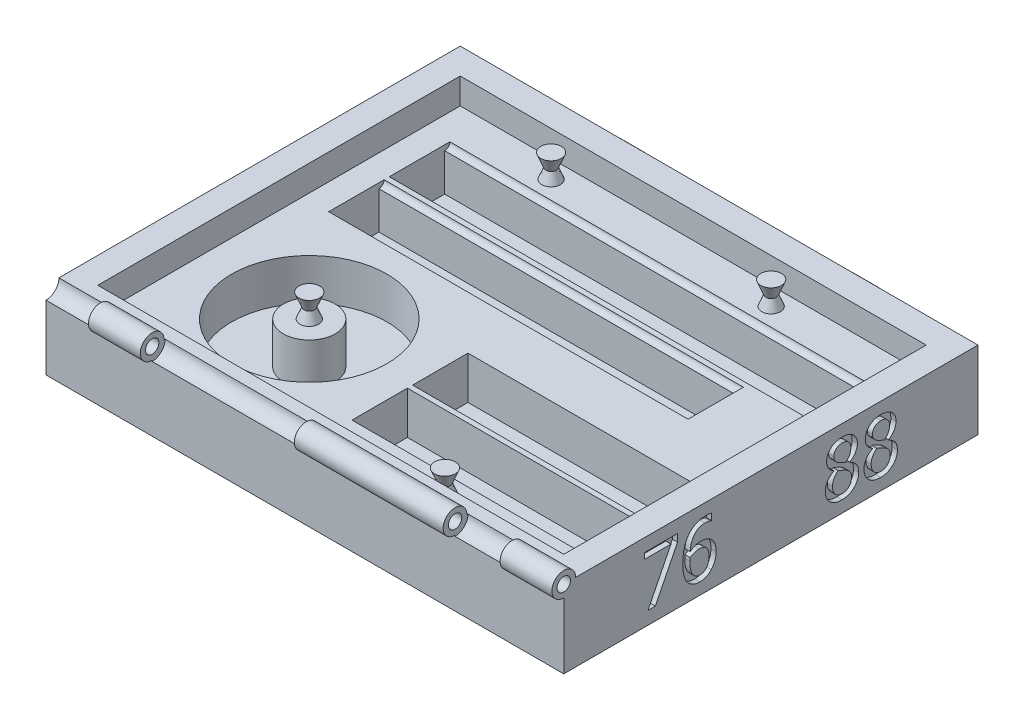
SolidWorks part; units mm, degrees
ref_plane "Front Plane" through (0, 0, 0) normal (0, 0, 1) x (1, 0, 0)
ref_plane "Top Plane" through (0, 0, 0) normal (0, 1, 0) x (1, 0, 0)
ref_plane "Right Plane" through (0, 0, 0) normal (1, 0, 0) x (0, 0, -1)
sketch "Sketch1" plane through (0, 0, 0) normal (0, 0, 1) x (1, 0, 0)
  line L0 (0, 0) -> (254, 0)
  line L1 (254, 0) -> (254, 101.6)
  line L2 (0, 0) -> (0, 101.6)
  line L3 (0, 101.6) -> (12.7, 101.6)
  line L4 (12.7, 101.6) -> (12.7, 25.4)
  line L5 (12.7, 25.4) -> (241.3, 25.4)
  line L6 (241.3, 25.4) -> (241.3, 101.6)
  line L7 (241.3, 101.6) -> (254, 101.6)
extrude "Boss-Extrude1" add sketch "Sketch1" along normal blind 177.8
sketch "Sketch2" plane through (0, 25.4, 0) normal (0, 1, 0) x (1, 0, 0)
  line L0 (228.6, -20.32) -> (25.4, -20.32)
  line L1 (241.3, -177.8) -> (12.7, -177.8) construction
  line L2 (241.3, 0) -> (12.7, 0) construction
  line L3 (228.6, -47.498) -> (228.6, -20.32)
  line L4 (25.4, -47.498) -> (228.6, -47.498)
  line L9 (201.676, -52.578) -> (25.4, -52.578)
  line L10 (201.676, -52.578) -> (201.676, -77.216)
  line L11 (201.676, -77.216) -> (25.4, -77.216)
  line L13 (228.6, -103.124) -> (119.634, -103.124)
  line L14 (228.6, -103.124) -> (228.6, -127.762)
  line L15 (228.6, -127.762) -> (119.634, -127.762)
  line L16 (25.4, -47.498) -> (25.4, -20.32)
  line L19 (228.6, -132.842) -> (119.634, -132.842)
  line L20 (228.6, -132.842) -> (228.6, -157.48)
  line L21 (25.4, -52.578) -> (25.4, -77.216)
  line L22 (119.634, -103.124) -> (119.634, -127.762)
  line L23 (119.634, -132.842) -> (119.634, -157.48)
  line L24 (119.634, -157.48) -> (228.6, -157.48)
  dimension "D1" = 5.08
  dimension "D2" = 20.32
  dimension "D3" = 5.08
  dimension "D4" = 20.32
  dimension "D5" = 0
extrude "Cut-Extrude1" cut sketch "Sketch2" against normal blind 12.7
sketch "Sketch3" plane through (228.6, 0, 0) normal (-1, 0, 0) x (0, 0, 1)
  circle A0 centre (157.48, 25.4) radius 3.81
  circle A1 centre (127.762, 25.4) radius 3.81
extrude "Cut-Extrude2" cut sketch "Sketch3" along normal blind 108.966
sketch "Sketch4" plane through (228.6, 0, 0) normal (-1, 0, 0) x (0, 0, 1)
  circle A0 centre (20.32, 25.4) radius 3.81
extrude "Cut-Extrude3" cut sketch "Sketch4" along normal blind 203.2
sketch "Sketch5" plane through (201.676, 0, 0) normal (-1, 0, 0) x (0, 0, 1)
  circle A0 centre (52.578, 25.4) radius 3.81
extrude "Cut-Extrude4" cut sketch "Sketch5" along normal blind 176.276
sketch "Sketch6" plane through (0, 12.7, 0) normal (0, 1, 0) x (1, 0, 0)
  line L0 (119.634, -132.842) -> (228.6, -132.842)
  line L1 (228.6, -132.842) -> (228.6, -157.48)
  line L2 (228.6, -157.48) -> (119.634, -157.48)
  line L3 (119.634, -157.48) -> (119.634, -132.842)
extrude "Cut-Extrude5" cut sketch "Sketch6" against normal blind 8.255
sketch "Sketch9" plane through (228.6, 0, 0) normal (-1, 0, 0) x (0, 0, 1)
  line L0 (157.48, 21.59) -> (157.48, 25.4)
  line L1 (157.48, 25.4) -> (161.29, 25.4)
  line L2 (161.29, 25.4) -> (161.29, 21.59)
  line L3 (161.29, 21.59) -> (157.48, 21.59)
  line L4 (127.762, 21.59) -> (127.762, 25.4)
  line L5 (127.762, 25.4) -> (131.572, 25.4)
  line L6 (131.572, 25.4) -> (131.572, 21.59)
  line L7 (131.572, 21.59) -> (127.762, 21.59)
  line L8 (48.768, 25.4) -> (52.578, 25.4)
  line L9 (52.578, 25.4) -> (52.578, 21.59)
  line L10 (52.578, 21.59) -> (48.768, 21.59)
  line L11 (48.768, 21.59) -> (48.768, 25.4)
  line L12 (16.51, 25.4) -> (20.32, 25.4)
  line L13 (20.32, 25.4) -> (20.32, 21.59)
  line L14 (20.32, 21.59) -> (16.51, 21.59)
  line L15 (16.51, 21.59) -> (16.51, 25.4)
extrude "Boss-Extrude2" add sketch "Sketch9" along normal blind 211.328
sketch "Sketch10" plane through (228.6, 0, 0) normal (-1, 0, 0) x (0, 0, 1)
  circle A0 centre (157.48, 25.4) radius 2.54
extrude "Cut-Extrude6" cut sketch "Sketch10" along normal blind 108.966
sketch "Sketch11" plane through (228.6, 0, 0) normal (-1, 0, 0) x (0, 0, 1)
  circle A0 centre (127.762, 25.4) radius 2.54
extrude "Cut-Extrude7" cut sketch "Sketch11" along normal blind 108.966
sketch "Sketch12" plane through (201.676, 0, 0) normal (-1, 0, 0) x (0, 0, 1)
  circle A0 centre (52.578, 25.4) radius 2.54
extrude "Cut-Extrude8" cut sketch "Sketch12" along normal blind 176.276
sketch "Sketch13" plane through (228.6, 0, 0) normal (-1, 0, 0) x (0, 0, 1)
  circle A0 centre (20.32, 25.4) radius 2.54
extrude "Cut-Extrude9" cut sketch "Sketch13" along normal blind 203.2
sketch "Sketch14" plane through (0, 12.7, 0) normal (0, 1, 0) x (1, 0, 0)
  line L0 (119.634, -127.762) -> (119.634, -103.124)
  line L1 (119.634, -103.124) -> (228.6, -103.124)
  line L2 (228.6, -103.124) -> (228.6, -127.762)
  line L3 (228.6, -127.762) -> (119.634, -127.762)
  line L4 (25.4, -77.216) -> (25.4, -52.578)
  line L5 (201.676, -52.578) -> (25.4, -52.578) construction
  line L6 (25.4, -50.038) -> (25.4, -77.216) construction
  line L7 (25.4, -52.578) -> (201.676, -52.578)
  line L8 (201.676, -52.578) -> (201.676, -77.216)
  line L9 (201.676, -77.216) -> (25.4, -77.216)
  line L10 (25.4, -47.498) -> (25.4, -20.32)
  line L11 (25.4, -20.32) -> (228.6, -20.32)
  line L12 (228.6, -47.498) -> (228.6, -17.78) construction
  line L13 (228.6, -47.498) -> (228.6, -20.32) construction
  line L14 (228.6, -20.32) -> (228.6, -47.498)
  line L15 (228.6, -47.498) -> (25.4, -47.498)
extrude "Cut-Extrude10" cut sketch "Sketch14" against normal blind 8.255
sketch "Sketch15" plane through (0, 0, 177.8) normal (0, 0, 1) x (1, 0, 0)
  line L0 (12.7, 25.4) -> (12.7, 50.8)
  line L1 (12.7, 25.4) -> (12.7, 101.6) construction
  line L2 (12.7, 50.8) -> (-40.623, 50.8)
  line L3 (-40.623, 50.8) -> (-40.623, 124.5264)
  line L4 (-40.623, 124.5264) -> (294.3288, 124.5264)
  line L5 (294.3288, 124.5264) -> (294.3288, 50.8)
  line L6 (294.3288, 50.8) -> (12.7, 50.8)
  line M2 (0, 101.6) -> (0, 0)
  line M4 (254, 0) -> (254, 101.6)
  line M5 (254, 101.6) -> (241.3, 101.6)
  line M6 (241.3, 101.6) -> (241.3, 25.4)
  line M8 (12.7, 25.4) -> (12.7, 101.6)
  line M9 (12.7, 101.6) -> (0, 101.6)
extrude "Cut-Extrude11" cut sketch "Sketch15" against normal blind 379.73 and the other way blind 44.45 contours L6 L5 L4 L3 L2 M2 M9 M8 M6 M5 M4 | L2 M8 M9 M2 | L6 M4 M5 M6
sketch "Sketch16" plane through (254, 0, 0) normal (1, 0, 0) x (0, 0, -1)
  line L0 (-177.8, 0) -> (-190.5, 0)
  line L1 (-190.5, 0) -> (-190.5, 50.8)
  line L2 (-177.8, 50.8) -> (-190.5, 50.8)
  line L7 (0, 0) -> (0, 50.8)
  line L8 (0, 50.8) -> (-177.8, 50.8)
  line L9 (-177.8, 50.8) -> (-177.8, 0)
  line L10 (-177.8, 0) -> (0, 0)
  line L13 (-177.8, 50.8) -> (-177.8, 0)
  dimension "D1" = 0
extrude "Boss-Extrude3" add sketch "Sketch16" against normal blind 254
sketch "Sketch17" plane through (254, 0, 0) normal (1, 0, 0) x (0, 0, -1)
  line L0 (0, 50.8) -> (12.7, 50.8)
  line L1 (12.7, 50.8) -> (12.7, 0)
  line L2 (12.7, 0) -> (0, 0)
  line L7 (0, 0) -> (0, 50.8)
  line L8 (0, 50.8) -> (-190.5, 50.8)
  line L9 (-190.5, 50.8) -> (-190.5, 0)
  line L10 (-190.5, 0) -> (0, 0)
  line L11 (0, 0) -> (0, 50.8)
  dimension "D1" = 0
extrude "Boss-Extrude4" add sketch "Sketch17" against normal blind 254
sketch "Sketch18" plane through (254, 0, 0) normal (1, 0, 0) x (0, 0, -1)
  line L0 (-190.5, 50.8) -> (12.7, 50.8)
  line L1 (12.7, 50.8) -> (12.7, 38.1)
  line L2 (12.7, 0) -> (12.7, 50.8) construction
  line L3 (12.7, 38.1) -> (-190.5, 38.1)
  line L4 (-190.5, 50.8) -> (-190.5, 0) construction
  line L5 (-190.5, 38.1) -> (-190.5, 50.8)
extrude "Cut-Extrude12" cut sketch "Sketch18" against normal blind 254
sketch "Sketch25" plane through (254, 0, 0) normal (1, 0, 0) x (0, 0, -1)
  text T0 "76" font "Tahoma" height 25.4
  text T1 "88" font "Tahoma" height 25.4
extrude "Cut-Extrude13" cut sketch "Sketch25" against normal blind 2.54
sketch "Sketch26" plane through (254, 0, 0) normal (1, 0, 0) x (0, 0, -1)
  circle A0 centre (-190.5, 38.1) radius 6.35
extrude "Cut-Extrude14" cut sketch "Sketch26" against normal blind 309.626
sketch "Sketch27" plane through (254, 0, 0) normal (1, 0, 0) x (0, 0, -1)
  line L0 (-184.658, 38.1) -> (-182.6014, 38.1)
  line L1 (-184.15, 38.1) -> (12.7, 38.1) construction
  line L2 (-182.6014, 38.1) -> (-185.679, 31.4435)
  line L3 (-185.679, 31.4435) -> (-190.5, 30.744)
  line L4 (-190.5, 31.75) -> (-190.5, 0) construction
  line L5 (-190.5, 30.744) -> (-190.5, 32.258)
  circle A0 centre (-190.5, 38.1) radius 5.842
  circle A1 centre (-190.5, 38.1) radius 3.302
  arc M27 (-184.15, 38.1) -> (-190.5, 31.75) centre (-190.5, 38.1) cw
extrude "Boss-Extrude7" add sketch "Sketch27" against normal blind 25.4 contours A0 L5 L0 M27 | A0 A1
sketch "Sketch28" plane through (0, 0, 190.5) normal (0, 0, 1) x (1, 0, 0)
  line L0 (254, 31.75) -> (200.66, 31.75)
  line L1 (0, 31.75) -> (228.6, 31.75) construction
ref_plane "Plane1" through (200.66, 0, 0) normal (1, 0, 0) x (0, 0, -1)
sketch "Sketch29" plane through (200.66, 0, 0) normal (1, 0, 0) x (0, 0, -1)
  line L0 (-184.658, 38.1) -> (-183.3065, 38.1)
  line L1 (-184.658, 38.1) -> (12.7, 38.1) construction
  line L2 (-183.3065, 38.1) -> (-185.019, 32.7769)
  line L3 (-185.019, 32.7769) -> (-188.6109, 30.9336)
  line L4 (-188.6109, 30.9336) -> (-190.5, 30.9336)
  line L5 (-190.5, 32.258) -> (-190.5, 0) construction
  line L6 (-190.5, 30.9336) -> (-190.5, 32.258)
  circle A0 centre (-190.5, 38.1) radius 3.302
  circle A1 centre (-190.5, 38.1) radius 5.842
extrude "Boss-Extrude8" add sketch "Sketch29" against normal blind 73.025 contours A1 L6 L4 L3 L2 L0 | A1 A0
sketch "Sketch30" plane through (0, 0, 190.5) normal (0, 0, 1) x (1, 0, 0)
  line L0 (0, 31.75) -> (26.67, 31.75)
  line L1 (0, 31.75) -> (127.635, 31.75) construction
ref_plane "Plane2" through (26.67, 0, 0) normal (-1, 0, 0) x (0, 0, 1)
sketch "Sketch31" plane through (26.67, 0, 0) normal (-1, 0, 0) x (0, 0, 1)
  line L0 (190.5, 32.258) -> (190.5, 30.6137)
  line L1 (190.5, 31.75) -> (190.5, 0) construction
  line L2 (190.5, 30.6137) -> (185.2632, 32.6776)
  line L3 (185.2632, 32.6776) -> (183.5935, 36.0403)
  line L4 (183.5935, 36.0403) -> (183.5935, 38.1)
  line L5 (184.15, 38.1) -> (-12.7, 38.1) construction
  line L6 (183.5935, 38.1) -> (184.658, 38.1)
  circle A0 centre (190.5, 38.1) radius 3.302
  circle A1 centre (190.5, 38.1) radius 5.842
extrude "Boss-Extrude9" add sketch "Sketch31" against normal blind 25.4 contours A1 L6 L4 L3 L2 L0 | A1 A0
sketch "Sketch35" plane through (0, 25.4, 0) normal (0, 1, 0) x (1, 0, 0)
  line L0 (25.4, -77.216) -> (201.676, -77.216) construction
  line L4 (241.3, -177.8) -> (12.7, -177.8) construction
  circle A0 centre (66.167, -127.508) radius 38.1
  dimension "D1" = 50.292
  dimension "D2" = 50.292
extrude "Cut-Extrude15" cut sketch "Sketch35" against normal blind 20.32
sketch "Sketch36" plane through (0, 5.08, 0) normal (0, 1, 0) x (1, 0, 0)
  circle A0 centre (66.167, -127.508) radius 12.7
extrude "Boss-Extrude11" add sketch "Sketch36" along normal blind 20.32
sketch "Sketch39" plane through (0, 25.4, 0) normal (0, 1, 0) x (1, 0, 0)
  line L0 (228.6, -160.02) -> (174.117, -160.02)
  line L1 (119.634, -160.02) -> (228.6, -160.02) construction
  line L2 (228.6, -17.78) -> (25.4, -17.78) construction
  circle A0 centre (174.117, -168.91) radius 2.54
  circle A1 centre (174.117, -8.89) radius 2.54
  circle A2 centre (66.167, -127.508) radius 5.08
  circle A3 centre (71.3117, -8.89) radius 5.08
  dimension "D1" = 8.89
extrude "Boss-Extrude12" add sketch "Sketch39" along normal blind 5.08 contours A1 | A0
sketch "Sketch47" plane through (0, 25.4, 0) normal (0, 1, 0) x (1, 0, 0)
  circle A0 centre (66.167, -127.508) radius 2.54
  circle A1 centre (66.167, -8.89) radius 2.54
extrude "Boss-Extrude13" add sketch "Sketch47" along normal blind 5.08
sketch "Sketch48" plane through (0, 0, -12.7) normal (0, 0, -1) x (-1, 0, 0)
  line L0 (-254, 0) -> (-177.8, 0)
  line L1 (0, 0) -> (-254, 0) construction
ref_plane "Plane3" through (177.8, 0, 0) normal (1, 0, 0) x (0, 0, -1)
sketch "Sketch49" plane through (177.8, 0, 0) normal (1, 0, 0) x (0, 0, -1)
  line L0 (12.7, 19.05) -> (12.7, 12.7)
  line L1 (12.7, 0) -> (12.7, 38.1) construction
  line L2 (12.7, 19.05) -> (12.7, 25.4)
  line L3 (12.7, 25.4) -> (22.86, 25.4)
  line L4 (12.7, 12.7) -> (22.86, 12.7)
  circle A0 centre (22.86, 19.05) radius 6.35
extrude "Boss-Extrude14" add sketch "Sketch49" along normal blind 12.7 contours A0 L3 L2 L0 L4 | A0
sketch "Sketch50" plane through (0, 0, -12.7) normal (0, 0, -1) x (-1, 0, 0)
  line L0 (0, 0) -> (-76.2, 0)
  line L1 (0, 0) -> (-254, 0) construction
ref_plane "Plane4" through (76.2, 0, 0) normal (-1, 0, 0) x (0, 0, 1)
sketch "Sketch51" plane through (76.2, 0, 0) normal (-1, 0, 0) x (0, 0, 1)
  line L0 (-12.7, 25.4) -> (-12.7, 12.7)
  line L1 (-12.7, 12.7) -> (-22.86, 12.7)
  line L2 (-12.7, 12.7) -> (-22.86, 12.7) construction
  line L3 (-12.7, 25.4) -> (-22.86, 25.4)
  circle A0 centre (-22.86, 19.05) radius 6.35
extrude "Boss-Extrude15" add sketch "Sketch51" along normal blind 12.7 contours A0 | A0 L1 L0 L3
sketch "Sketch52" plane through (190.5, 0, 0) normal (1, 0, 0) x (0, 0, -1)
  circle A0 centre (22.86, 19.05) radius 3.81
extrude "Cut-Extrude16" cut sketch "Sketch52" against normal blind 137.16
fillet "Fillet1" radius 5.08 4 edges at (69.85, 12.7, -12.7) (184.15, 12.7, -12.7) (69.85, 25.4, -12.7) (184.15, 25.4, -12.7)
sketch "Sketch53" plane through (0, 30.48, 0) normal (0, 1, 0) x (1, 0, 0)
  line L0 (66.167, -11.43) -> (66.167, -8.89)
  circle A0 centre (66.167, -8.89) radius 2.54 construction
ref_plane "Plane5" through (66.167, 0, 0) normal (-1, 0, 0) x (0, 0, 1)
sketch "Sketch54" plane through (66.167, 0, 0) normal (-1, 0, 0) x (0, 0, 1)
  line L0 (8.89, 24.13) -> (8.89, 36.83)
  line L1 (11.43, 30.48) -> (8.89, 30.48) construction
  line L2 (8.89, 36.83) -> (13.97, 36.83)
  line L4 (11.43, 30.48) -> (13.97, 36.83)
  line L6 (8.89, 24.13) -> (13.97, 24.13)
  line L7 (11.43, 30.48) -> (13.97, 24.13)
revolve "Revolve2" add sketch "Sketch54" angle 360 about L0
sketch "Sketch58" plane through (0, 30.48, 0) normal (0, 1, 0) x (1, 0, 0)
  line L0 (66.167, -127.508) -> (66.167, -130.048)
  circle A0 centre (66.167, -127.508) radius 2.54 construction
sketch "Sketch59" plane through (66.167, 0, 0) normal (-1, 0, 0) x (0, 0, 1)
  line L0 (127.508, 30.48) -> (127.508, 36.83)
  line L2 (127.508, 30.48) -> (130.048, 30.48) construction
  line L3 (127.508, 36.83) -> (132.588, 36.83)
  line L4 (132.588, 36.83) -> (130.048, 30.48)
  line L5 (127.508, 30.48) -> (127.508, 24.13)
  line L6 (132.588, 24.13) -> (130.048, 30.48)
  line L7 (127.508, 24.13) -> (132.588, 24.13)
revolve "Revolve4" add sketch "Sketch59" angle 360 about L0
sketch "Sketch60" plane through (0, 30.48, 0) normal (0, 1, 0) x (1, 0, 0)
  line L0 (174.117, -11.43) -> (174.117, -8.89)
  circle A0 centre (174.117, -8.89) radius 2.54 construction
ref_plane "Plane6" through (174.117, 0, 0) normal (1, 0, 0) x (0, 0, -1)
sketch "Sketch61" plane through (174.117, 0, 0) normal (1, 0, 0) x (0, 0, -1)
  line L1 (-11.43, 30.48) -> (-8.89, 30.48) construction
  line L2 (-8.89, 24.13) -> (-8.89, 36.83)
  line L3 (-8.89, 36.83) -> (-13.97, 36.83)
  line L4 (-13.97, 36.83) -> (-11.43, 30.48)
  line L5 (-8.89, 24.13) -> (-13.97, 24.13)
  line L6 (-13.97, 24.13) -> (-11.43, 30.48)
revolve "Revolve5" add sketch "Sketch61" angle 360 about L2
sketch "Sketch62" plane through (0, 30.48, 0) normal (0, 1, 0) x (1, 0, 0)
  line L0 (174.117, -168.91) -> (174.117, -171.45)
  circle A0 centre (174.117, -168.91) radius 2.54 construction
sketch "Sketch63" plane through (174.117, 0, 0) normal (1, 0, 0) x (0, 0, -1)
  line L1 (-168.91, 24.13) -> (-168.91, 36.83)
  line L2 (-168.91, 36.83) -> (-173.99, 36.83)
  line L3 (-173.99, 36.83) -> (-171.45, 30.48)
  line L4 (-168.91, 24.13) -> (-173.99, 24.13)
  line L5 (-173.99, 24.13) -> (-171.45, 30.48)
revolve "Revolve6" add sketch "Sketch63" angle 360 about L1
